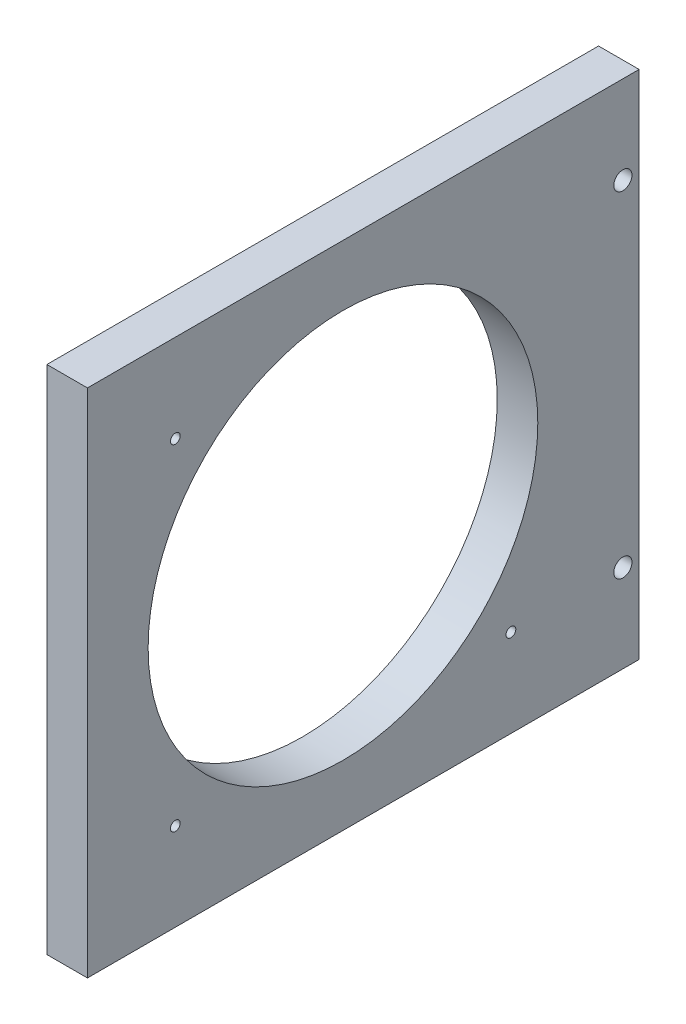
SolidWorks part; units mm, degrees
ref_plane "Front Plane" through (0, 0, 0) normal (0, 0, 1) x (1, 0, 0)
ref_plane "Top Plane" through (0, 0, 0) normal (0, 1, 0) x (1, 0, 0)
ref_plane "Right Plane" through (0, 0, 0) normal (1, 0, 0) x (0, 0, -1)
sketch "Sketch1" plane through (0, 0, 0) normal (1, 0, 0) x (0, 0, -1)
  line L0 (0, 40) -> (86.36, 40) construction
  line L1 (0, 0) -> (86.36, 0)
  line L2 (0, 0) -> (0, 80)
  line L3 (0, 80) -> (86.36, 80)
  line L4 (86.36, 0) -> (86.36, 80)
  line L5 (43.18, 80) -> (43.18, 0) construction
  circle A0 centre (40, 40) radius 30.5
  dimension "D1" = 80
  dimension "D2" = 86.36
extrude "Boss-Extrude1" add sketch "Sketch1" along normal blind 6.35
sketch "Sketch3" plane through (0, 0, 0) normal (-1, 0, 0) x (0, 0, 1)
  line L0 (0, 40) -> (-86.36, 40) construction
  line L1 (0, 80) -> (0, 0) construction
  line L2 (-86.36, 0) -> (-86.36, 80) construction
  line L3 (-40.0236, 0) -> (-40.0236, 80) construction
  line L5 (0, 0) -> (-86.36, 0) construction
  line L6 (-86.36, 80) -> (0, 80) construction
  circle A0 centre (-66.2926, 13.75) radius 0.762
  circle A1 centre (-13.7547, 13.75) radius 0.762
  circle A3 centre (-13.7547, 66.25) radius 0.762
  circle A4 centre (-83.82, 13.75) radius 1.4224
  circle A5 centre (-83.82, 66.25) radius 1.4224
extrude "Cut-Extrude2" cut sketch "Sketch3" against normal blind 6.35
